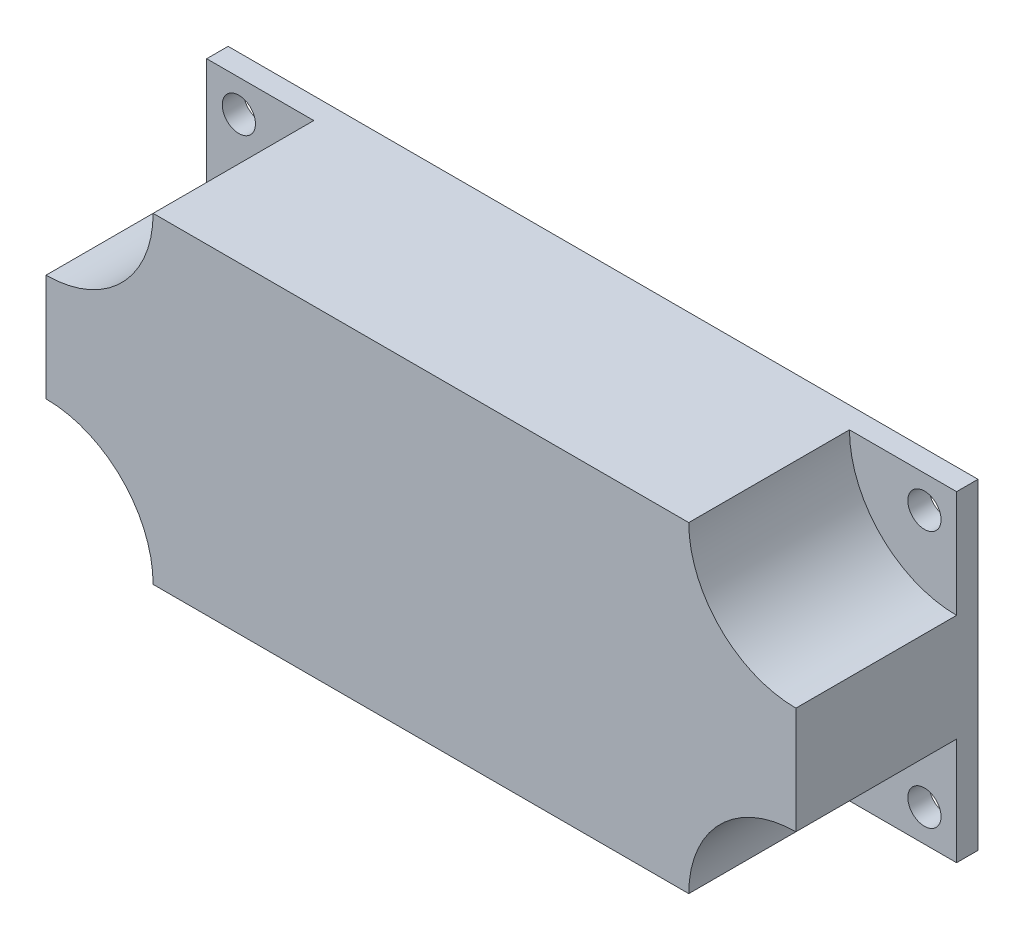
SolidWorks part; units mm, degrees
ref_plane "Front Plane" through (0, 0, 0) normal (0, 0, 1) x (1, 0, 0)
ref_plane "Top Plane" through (0, 0, 0) normal (0, 1, 0) x (1, 0, 0)
ref_plane "Right Plane" through (0, 0, 0) normal (1, 0, 0) x (0, 0, -1)
sketch "Sketch1" plane through (0, 0, 0) normal (0, 0, 1) x (1, 0, 0)
  line L1 (-35, 15) -> (35, 15)
  line L2 (-35, 15) -> (-35, -15)
  line L3 (-35, -15) -> (35, -15)
  line L4 (35, 15) -> (35, -15)
  line L5 (-35, 15) -> (35, -15) construction
  line L6 (-35, -15) -> (35, 15) construction
  line L7 (-32, 12) -> (32, 12) construction
  line L8 (-32, 12) -> (-32, -12) construction
  line L9 (-32, -12) -> (32, -12) construction
  line L10 (32, 12) -> (32, -12) construction
  line L11 (-32, 12) -> (32, -12) construction
  line L12 (-32, -12) -> (32, 12) construction
  circle A0 centre (-32, 12) radius 1.55
  circle A1 centre (32, 12) radius 1.55
  circle A2 centre (32, -12) radius 1.55
  circle A3 centre (-32, -12) radius 1.55
  point P0 (0, 0)
  point P6 (0, 0)
  dimension "D5" = 3.1
  dimension "D6" = 3.1
  dimension "D7" = 3.1
  dimension "D8" = 3.1
  dimension "D1" = 70
  dimension "D2" = 30
  dimension "D3" = 64
  dimension "D4" = 24
extrude "Boss-Extrude1" add sketch "Sketch1" along normal blind 17
sketch "Sketch2" plane through (0, 0, 17) normal (0, 0, 1) x (1, 0, 0)
  line L0 (35, 15) -> (-35, 15) construction
  line L1 (-35, 15) -> (-35, -15) construction
  line L2 (-35, -15) -> (35, -15) construction
  line L3 (35, -15) -> (35, 15) construction
  line L4 (-35, 5) -> (-35, 15)
  line L5 (-35, 15) -> (-25, 15)
  line L6 (-25, 15) -> (-25.0643, 14.9649)
  line L7 (25, 15) -> (35, 15)
  line L8 (35, 15) -> (35, 5)
  line L9 (35, -5) -> (35, -15)
  line L10 (35, -15) -> (25, -15)
  line L11 (-25, -15) -> (-35, -15)
  line L12 (-35, -15) -> (-35, -5)
  arc A0 (-25, 15) -> (-35, 5) centre (-35, 15) cw
  arc A1 (-35, -5) -> (-25, -15) centre (-35, -15) cw
  arc A2 (25, -15) -> (35, -5) centre (35, -15) cw
  arc A3 (25, 15) -> (35, 5) centre (35, 15) ccw
  dimension "D1" = 10
  dimension "D2" = 10
  dimension "D3" = 10
  dimension "D4" = 10
extrude "Cut-Extrude1" cut sketch "Sketch2" against normal blind 15
